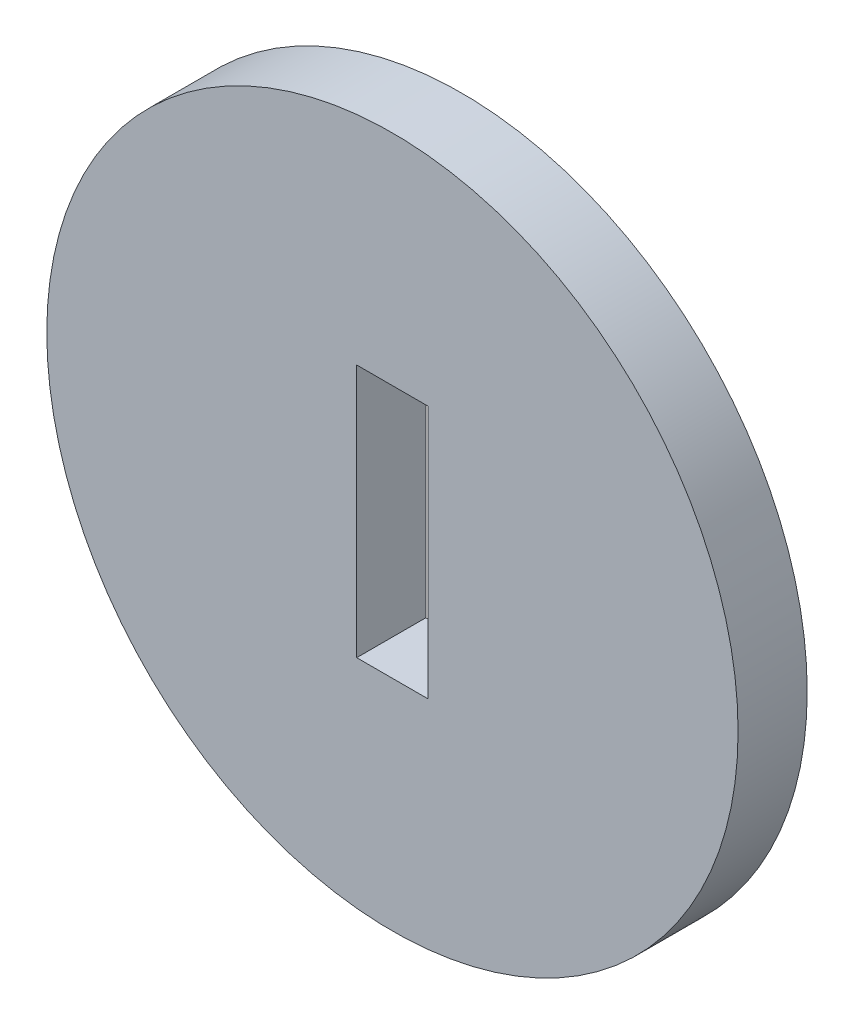
SolidWorks part; units mm, degrees
ref_plane "Front Plane" through (0, 0, 0) normal (0, 0, 1) x (1, 0, 0)
ref_plane "Top Plane" through (0, 0, 0) normal (0, 1, 0) x (1, 0, 0)
ref_plane "Right Plane" through (0, 0, 0) normal (1, 0, 0) x (0, 0, -1)
sketch "Sketch1" plane through (0, 0, 0) normal (0, 0, 1) x (1, 0, 0)
  circle A0 centre (0, 0) radius 15
  dimension "D1" = 30
extrude "Boss-Extrude1" add sketch "Sketch1" along normal blind 3
sketch "Sketch3" plane through (0, 0, 0) normal (0, 0, 1) x (1, 0, 0)
  line L1 (-1.55, 5.5) -> (1.55, 5.5)
  line L2 (-1.55, 5.5) -> (-1.55, -5.5)
  line L3 (-1.55, -5.5) -> (1.55, -5.5)
  line L4 (1.55, 5.5) -> (1.55, -5.5)
  line L5 (-1.55, 5.5) -> (1.55, -5.5) construction
  line L6 (-1.55, -5.5) -> (1.55, 5.5) construction
  point P0 (0, 0)
  dimension "D1" = 3.1
  dimension "D2" = 11
extrude "Cut-Extrude1" cut sketch "Sketch3" along normal blind 3 contours L4 L3 L2 L1
